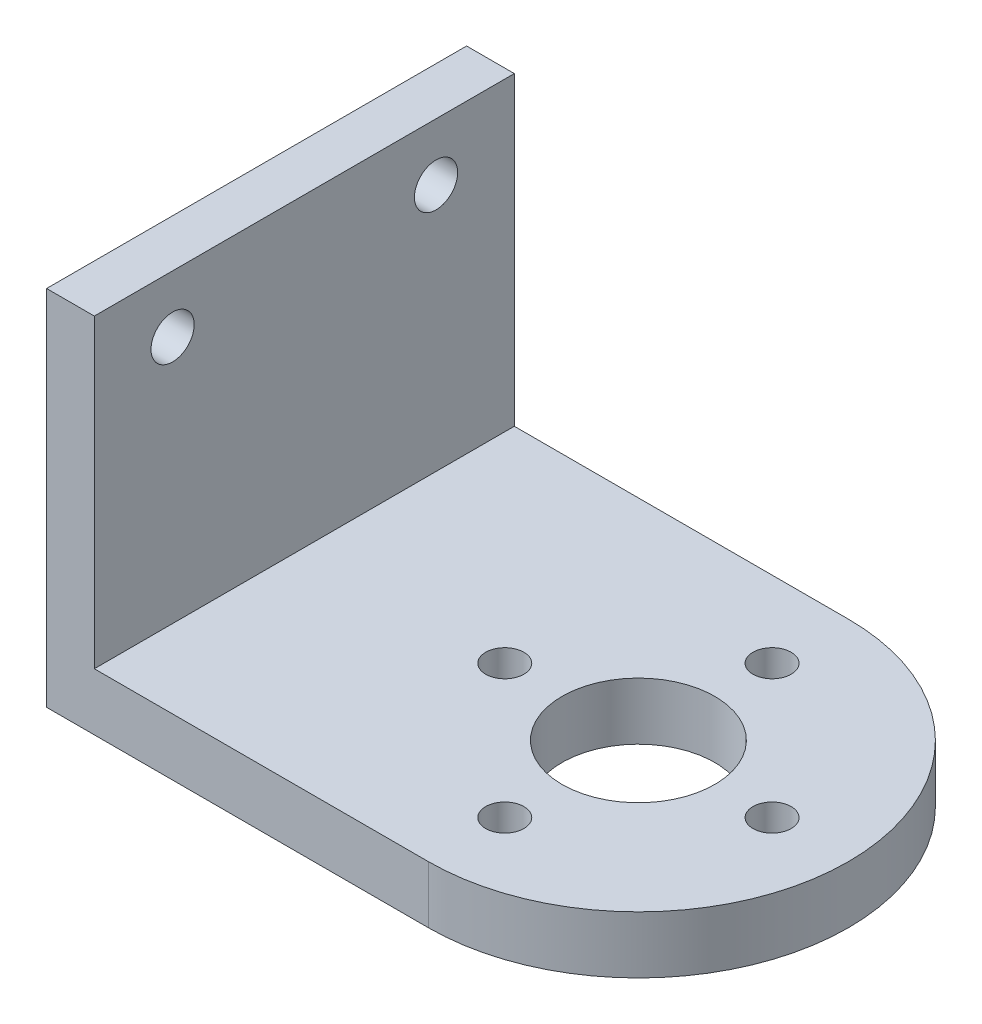
SolidWorks part; units mm, degrees
ref_plane "Front Plane" through (0, 0, 0) normal (0, 0, 1) x (1, 0, 0)
ref_plane "Top Plane" through (0, 0, 0) normal (0, 1, 0) x (1, 0, 0)
ref_plane "Right Plane" through (0, 0, 0) normal (1, 0, 0) x (0, 0, -1)
sketch "Sketch1" plane through (0, 0, 0) normal (0, 1, 0) x (1, 0, 0)
  line L0 (-28.2208, 0) -> (26.2745, 0) construction
  line L2 (-14, -11) -> (-14, 11)
  line L5 (-14, 11) -> (6, 11)
  line L6 (6, -11) -> (-14, -11)
  circle A0 centre (6, -7) radius 1
  circle A1 centre (-1, 0) radius 1
  circle A2 centre (6, 0) radius 4
  arc A3 (6, -11) -> (6, 11) centre (6, 0) ccw
  circle A4 centre (13, 0) radius 1
  circle A5 centre (6, 7) radius 1
  point P0 (0, 0)
  point P6 (-14, 0)
  point P22 (6, 0)
  dimension "D3" = 8
  dimension "D5" = 22
  dimension "D6" = 4
  dimension "D12" = 2
  dimension "D2" = 22
  dimension "D4" = 20
  dimension "D11" = 7
extrude "Boss-Extrude1" add sketch "Sketch1" along normal blind 3
sketch "Sketch2" plane through (0, 3, 0) normal (0, 1, 0) x (1, 0, 0)
  line L0 (-14, 11) -> (-11.5, 11)
  line L1 (6, 11) -> (-14, 11) construction
  line L2 (-11.5, 11) -> (-11.5, -11)
  line L3 (-14, -11) -> (6, -11) construction
  line L4 (-11.5, -11) -> (-14, -11)
  line L5 (-14, 11) -> (-14, -11)
  dimension "D1" = 2.5
extrude "Boss-Extrude2" add sketch "Sketch2" along normal blind 16
sketch "Sketch3" plane through (-11.5, 0, 0) normal (1, 0, 0) x (0, 0, -1)
  line L0 (11, 19) -> (11, 3) construction
  line L1 (-11, 19) -> (11, 19) construction
  line L2 (-11, 19) -> (-11, 3) construction
  circle A0 centre (6.9, 16) radius 1.1324
  circle A1 centre (-6.9, 16) radius 1.131
  point P6 (11, 11)
  point P11 (-11, 11)
  dimension "D1" = 4.1
  dimension "D2" = 3
  dimension "D3" = 4.1
  dimension "D4" = 3
extrude "Cut-Extrude1" cut sketch "Sketch3" against normal blind 6
